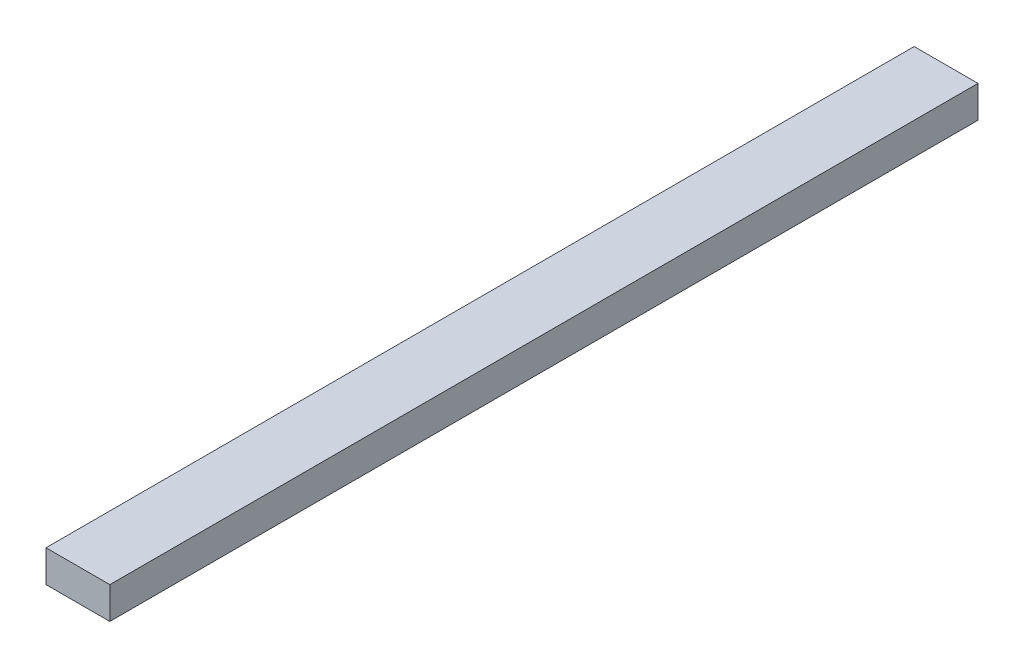
SolidWorks part; units mm, degrees
ref_plane "Front Plane" through (0, 0, 0) normal (0, 0, 1) x (1, 0, 0)
ref_plane "Top Plane" through (0, 0, 0) normal (0, 1, 0) x (1, 0, 0)
ref_plane "Right Plane" through (0, 0, 0) normal (1, 0, 0) x (0, 0, -1)
sketch "Sketch1" plane through (0, 0, 0) normal (0, 0, 1) x (1, 0, 0)
  line L1 (0, 0) -> (12.7, 0)
  line L2 (0, 0) -> (0, 6.35)
  line L3 (0, 6.35) -> (12.7, 6.35)
  line L4 (12.7, 0) -> (12.7, 6.35)
extrude "Boss-Extrude1" add sketch "Sketch1" along normal blind 172.72
sketch "Sketch2" plane through (0, 0, 172.72) normal (0, 0, 1) x (1, 0, 0)
  line L0 (0, 3.175) -> (12.7, 3.175) construction
  line L1 (0, 6.35) -> (0, 0) construction
  line L2 (12.7, 0) -> (12.7, 6.35) construction
  line L3 (6.35, 6.35) -> (6.35, 0) construction
  line L4 (12.7, 6.35) -> (0, 6.35) construction
  line L5 (0, 0) -> (12.7, 0) construction
